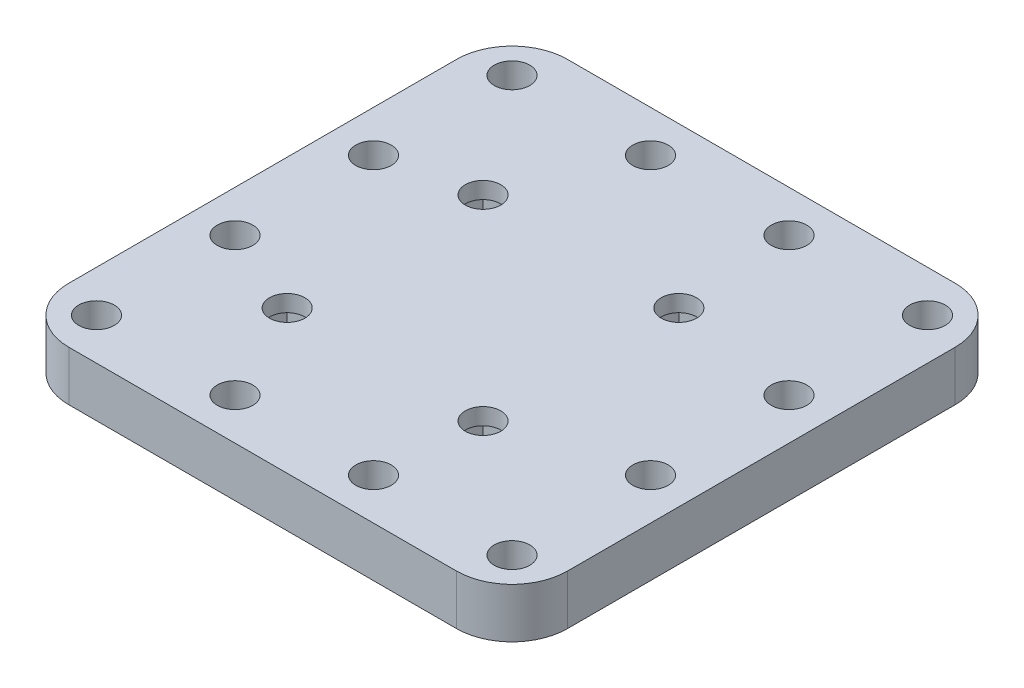
SolidWorks part; units mm, degrees
ref_plane "정면" through (0, 0, 0) normal (0, 0, 1) x (1, 0, 0)
ref_plane "윗면" through (0, 0, 0) normal (0, 1, 0) x (1, 0, 0)
ref_plane "우측면" through (0, 0, 0) normal (1, 0, 0) x (0, 0, -1)
sketch "스케치1" plane through (0, 0, 0) normal (0, 1, 0) x (1, 0, 0)
  line L0 (8.75, 58.75) -> (-25, 50) construction
  line L1 (8.75, 58.75) -> (-50, 25) construction
  line L2 (8.75, 58.75) -> (-25, 0) construction
  line L3 (8.75, 58.75) -> (0, 25) construction
  line L4 (8.75, 58.75) -> (-8.9277, 28.698) construction
  line L5 (8.75, 58.75) -> (-8.9277, -6.6574) construction
  line L6 (8.75, 58.75) -> (26.4277, -6.6574) construction
  line L7 (8.75, 58.75) -> (26.4277, 28.698) construction
  line L8 (26.4277, 28.698) -> (26.4277, -6.6574) construction
  line L9 (26.4277, -6.6574) -> (-8.9277, -6.6574) construction
  line L10 (-8.9277, -6.6574) -> (-8.9277, 28.698) construction
  line L11 (-8.9277, 28.698) -> (26.4277, 28.698) construction
  line L12 (57.5, 57.5) -> (-32.5, 57.5)
  line L13 (-32.5, 57.5) -> (-32.5, -32.5)
  line L15 (-32.5, -32.5) -> (57.5, -32.5)
  line L16 (57.5, 57.5) -> (57.5, -32.5)
  circle A0 centre (-8.9277, 28.698) radius 3.2
  circle A1 centre (26.4277, 28.698) radius 3.2
  circle A2 centre (-8.9277, -6.6574) radius 3.2
  circle A3 centre (26.4277, -6.6574) radius 3.2
  circle A4 centre (25, -25) radius 3.2
  circle A5 centre (50, 25) radius 3.2
  circle A6 centre (50, -25) radius 3.2
  circle A7 centre (0, -25) radius 3.2
  circle A8 centre (50, 50) radius 3.2
  circle A9 centre (-25, 50) radius 3.2
  circle A10 centre (-25, -25) radius 3.2
  circle A11 centre (-25, 25) radius 3.2
  circle A12 centre (-25, 0) radius 3.2
  circle A13 centre (50, 0) radius 3.2
  circle A14 centre (25, 50) radius 3.2
  circle A15 centre (0, 50) radius 3.2
  point P0 (-50, 0)
  point P1 (8.75, 58.75)
  point P3 (-25, 50)
  point P4 (0, 25)
  point P7 (0, 50)
  point P8 (0, 0)
  point P10 (-50, 50)
  point P11 (-25, 0)
  point P12 (-50, 25)
  point P22 (0, 0)
  dimension "D1" = 50
  dimension "D3" = 25
  dimension "D11" = 6.4
  dimension "D15" = 7.5
  dimension "D14" = 6.4
  dimension "D28" = 25
  dimension "D2" = 50
  dimension "D4" = 25
  dimension "D5" = 8.75
  dimension "D6" = 8.75
  dimension "D7" = 45
  dimension "D8" = 45
  dimension "D9" = 45
  dimension "D10" = 45
  dimension "D12" = 50
  dimension "D13" = 50
  dimension "D16" = 7.5
  dimension "D17" = 7.5
  dimension "D18" = 7.5
  dimension "D23" = 25
  dimension "D24" = 75
  dimension "D25" = 75
  dimension "D26" = 25
  dimension "D27" = 25
  dimension "D29" = 25
  dimension "D30" = 25
  dimension "D31" = 25
extrude "보스-돌출1" add sketch "스케치1" along normal blind 9
sketch "스케치2" plane through (0, 0, 0) normal (0, -1, 0) x (1, 0, 0)
  line L1 (-14.0777, 11.8074) -> (-3.7777, 11.8074)
  line L2 (-14.0777, 11.8074) -> (-14.0777, 1.5074)
  line L3 (-14.0777, 1.5074) -> (-3.7777, 1.5074)
  line L4 (-3.7777, 11.8074) -> (-3.7777, 1.5074)
  line L5 (21.2777, 11.8074) -> (31.5777, 11.8074)
  line L6 (21.2777, 11.8074) -> (21.2777, 1.5074)
  line L7 (21.2777, 1.5074) -> (31.5777, 1.5074)
  line L8 (31.5777, 11.8074) -> (31.5777, 1.5074)
  line L9 (21.2777, -23.548) -> (31.5777, -23.548)
  line L10 (21.2777, -23.548) -> (21.2777, -33.848)
  line L11 (21.2777, -33.848) -> (31.5777, -33.848)
  line L12 (31.5777, -23.548) -> (31.5777, -33.848)
  line L13 (-14.0777, -23.548) -> (-3.7777, -23.548)
  line L14 (-14.0777, -23.548) -> (-14.0777, -33.848)
  line L15 (-14.0777, -33.848) -> (-3.7777, -33.848)
  line L16 (-3.7777, -23.548) -> (-3.7777, -33.848)
  point P16 (-8.9277, 6.6574)
  point P17 (-8.9277, -28.698)
  point P18 (26.4277, -28.698)
  point P19 (26.4277, 6.6574)
  point P23 (0, 0)
  point P25 (-8.9277, 11.8074)
  point P26 (-3.7777, 6.6574)
  point P27 (-8.9277, -23.548)
  point P28 (-3.7777, -28.698)
  point P29 (0, 0)
  point P30 (26.4277, -23.548)
  point P31 (0, 0)
  point P32 (21.2777, -28.698)
  point P33 (0, 0)
  point P34 (31.5777, 6.6574)
  point P35 (26.4277, 11.8074)
  dimension "D1" = 10.3
extrude "컷-돌출1" cut sketch "스케치2" against normal offset from surface (6 mm away) 3 up to face at (12.5, 9, -12.5)
fillet "필렛1" radius 10 4 edges at (57.5, 4.5, -57.5) (57.5, 4.5, 32.5) (-32.5, 4.5, 32.5) (-32.5, 4.5, -57.5)
